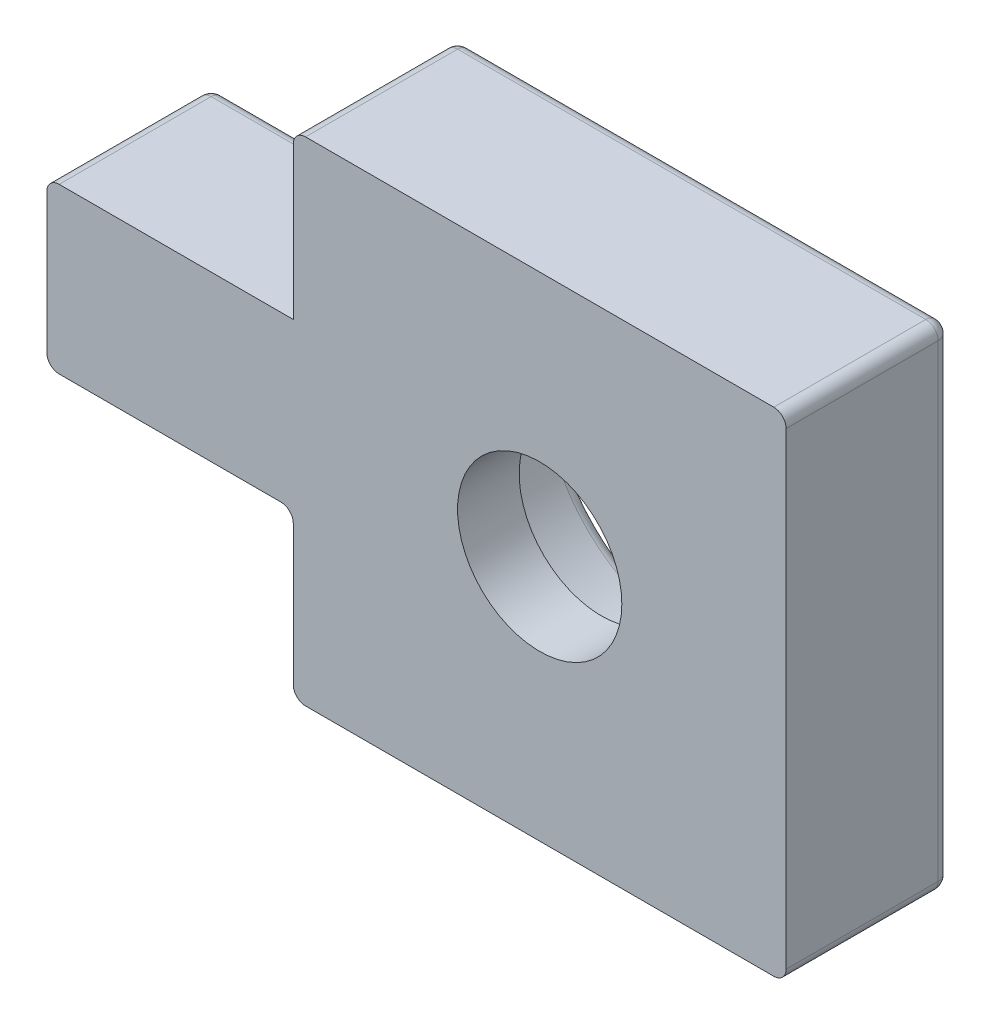
SolidWorks part; units mm, degrees
ref_plane "Front" through (0, 0, 0) normal (0, 0, 1) x (1, 0, 0)
ref_plane "Top" through (0, 0, 0) normal (0, 1, 0) x (1, 0, 0)
ref_plane "Right" through (0, 0, 0) normal (1, 0, 0) x (0, 0, -1)
sketch "Esquisse1" plane through (0, 0, 0) normal (0, 0, 1) x (1, 0, 0)
  line L1 (0, 0) -> (12, 0)
  line L2 (0, 0) -> (0, 12)
  line L3 (0, 12) -> (12, 12)
  line L4 (12, 0) -> (12, 12)
  dimension "D1" = 12
  dimension "D2" = 12
extrude "Boss.-Extru.1" add sketch "Esquisse1" along normal blind 4
sketch "Esquisse2" plane through (0, 0, 0) normal (0, 0, 1) x (1, 0, 0)
  line L0 (0, 0) -> (12, 0) construction
  line L2 (12, 0) -> (12, 12) construction
  circle A0 centre (6, 6) radius 2
  point P6 (4.7447, 10.3283)
  point P7 (12, 3.2168)
  dimension "D1" = 4
  dimension "D2" = 6
  dimension "D3" = 6
extrude "Enlèv. mat.-Extru.2" cut sketch "Esquisse2" along normal blind 4
sketch "Esquisse3" plane through (0, 0, 0) normal (0, 0, 1) x (1, 0, 0)
  circle A0 centre (6, 6) radius 3.6
  circle A1 centre (6, 6) radius 2 construction
  dimension "D1" = 7.2
extrude "Enlèv. mat.-Extru.3" cut sketch "Esquisse3" along normal blind 2.5
sketch "Esquisse4" plane through (0, 0, 0) normal (0, 0, 1) x (1, 0, 0)
  line L0 (0, 12) -> (0, 0) construction
  line L1 (0, 8) -> (-6, 8)
  line L2 (0, 8) -> (0, 4)
  line L3 (0, 4) -> (-6, 4)
  line L4 (-6, 8) -> (-6, 4)
  line L5 (12, 12) -> (0, 12) construction
  dimension "D1" = 4
  dimension "D2" = 4
  dimension "D3" = 6
extrude "Boss.-Extru.2" add sketch "Esquisse4" along normal blind 4
sketch "Esquisse5" plane through (0, 0, 0) normal (0, 0, 1) x (1, 0, 0)
  line L0 (-6, 4) -> (0, 4) construction
  line L1 (-6, 8) -> (-6, 4) construction
  circle A0 centre (-4, 6) radius 1.25
  dimension "D1" = 2.5
  dimension "D2" = 2
  dimension "D3" = 2
extrude "Boss.-Extru.3" add sketch "Esquisse5" against normal blind 4 draft 2
chamfer "Chanfrein1" distance 0.5 angle 45 1 edges at (-2.8897, 6, -4)
fillet "Congé1" radius 0.3 17 edges at (-3, 8, 0) (-6, 6, 0) (-3, 4, 0) (0, 2, 0) (6, 0, 0) (12, 6, 0) (6, 12, 0) (0, 10, 0) (9.6, 6, 0) (-5.25, 6, 0) (-6, 8, 2) (0, 12, 2) (12, 12, 2) (12, 0, 2) (-6, 4, 2) (0, 4, 2) (0, 0, 2)
